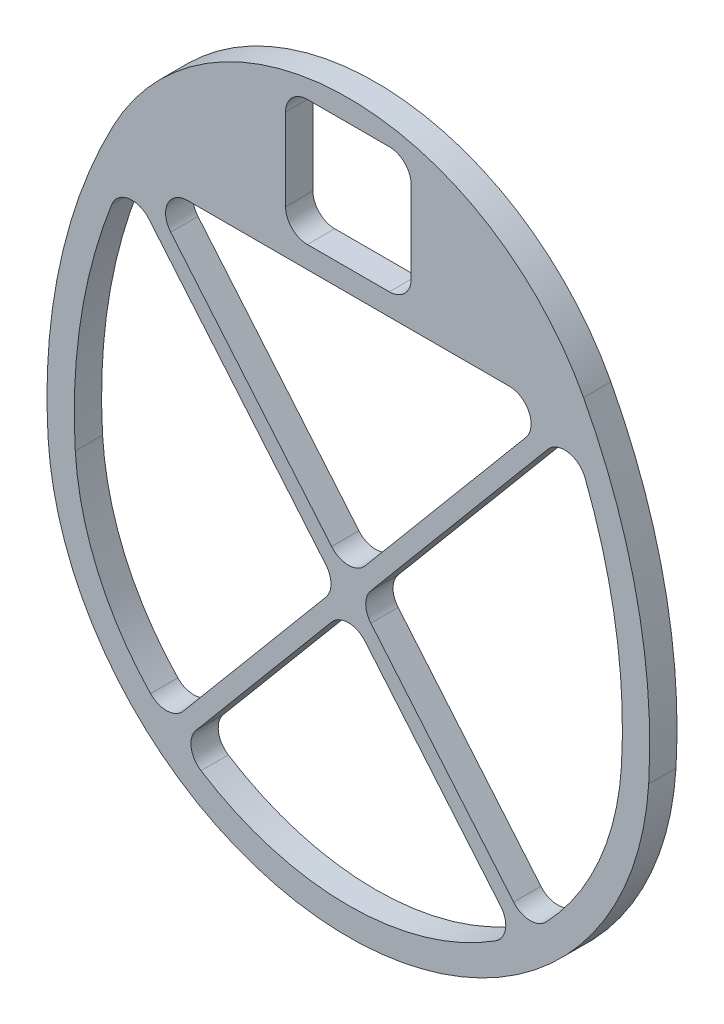
SolidWorks part; units mm, degrees
material "Balsa"
ref_plane "Front Plane" through (0, 0, 0) normal (0, 0, 1) x (1, 0, 0)
ref_plane "Top Plane" through (0, 0, 0) normal (0, 1, 0) x (1, 0, 0)
ref_plane "Right Plane" through (0, 0, 0) normal (1, 0, 0) x (0, 0, -1)
sketch "Sketch1" plane through (0, 0, 0) normal (0, 0, 1) x (1, 0, 0)
  line L8 (-63.5, 0) -> (63.5, 0) construction
  line L9 (-54.6952, 69.85) -> (54.6952, 69.85)
  line L10 (-50.8, 63.5) -> (50.8, 63.5)
  line L21 (-69.8384, -0.3833) -> (-63.5, 0)
  line L22 (63.5, 0) -> (69.8384, -0.3833)
  arc A0 (50.8, 63.5) -> (63.5, 0) centre (-63.2684, 7.6663) cw
  arc A1 (-50.8, 63.5) -> (-63.5, 0) centre (63.2684, 7.6663) ccw
  arc A2 (-54.6952, 69.85) -> (-69.8384, -0.3833) centre (63.2684, 7.6663) ccw
  arc A3 (54.6952, 69.85) -> (69.8384, -0.3833) centre (-63.2684, 7.6663) cw
  arc A4 (-56.5034, 66.2917) -> (-69.8384, -0.3833) centre (63.2684, 7.6663) ccw construction
  arc A5 (56.5034, 66.2917) -> (69.8384, -0.3833) centre (-63.2684, 7.6663) cw construction
  arc A6 (50.8, 63.5) -> (63.5, 0) centre (-63.2684, 7.6663) cw construction
  arc A7 (-50.8, 63.5) -> (-63.5, 0) centre (63.2684, 7.6663) ccw construction
  arc A8 (-54.6952, 69.85) -> (54.6952, 69.85) centre (0, 41.0178) cw
  arc A9 (-63.5, 0) -> (63.5, 0) centre (0, 3.8402) ccw
  arc A10 (-69.8384, -0.3833) -> (69.8384, -0.3833) centre (0, 3.8402) ccw
  point P0 (0, 0)
  point P13 (0, 63.5)
  dimension "D7" = 127
  dimension "D2" = 127
  dimension "D3" = 63.5
  dimension "D6" = 101.6
  dimension "D1" = 6.35
  dimension "D4" = 6.35
  dimension "D5" = 6.35
extrude "Boss-Extrude1" add sketch "Sketch1" along normal blind 6.35
sketch "Sketch2" plane through (0, 0, 6.35) normal (0, 0, 1) x (1, 0, 0)
  line L0 (0, 63.5) -> (0, 102.8471) construction
  line L1 (-14.605, 97.7785) -> (14.605, 97.7785)
  line L2 (-14.605, 97.7785) -> (-14.605, 68.5685)
  line L3 (-14.605, 68.5685) -> (14.605, 68.5685)
  line L4 (14.605, 97.7785) -> (14.605, 68.5685)
  line L5 (-14.605, 97.7785) -> (14.605, 68.5685) construction
  line L6 (-14.605, 68.5685) -> (14.605, 97.7785) construction
  line L7 (-50.8, 63.5) -> (50.8, 63.5) construction
  arc A0 (54.6952, 69.85) -> (-54.6952, 69.85) centre (0, 41.0178) ccw construction
  point P0 (0, 83.1735)
  point P15 (0, 83.1735)
  dimension "D1" = 29.21
  dimension "D2" = 29.21
extrude "Cut-Extrude1" cut sketch "Sketch2" against normal up to next
fillet "Fillet1" radius 5.08 4 edges at (14.605, 68.5685, 3.175) (14.605, 97.7785, 3.175) (-14.605, 97.7785, 3.175) (-14.605, 68.5685, 3.175)
sketch "Sketch3" plane through (0, 0, 6.35) normal (0, 0, 1) x (1, 0, 0)
  line L0 (-52.2593, 62.2755) -> (-49.3407, 64.7245)
  line L1 (-52.2593, 62.2755) -> (40.8035, -48.6324)
  line L2 (-49.3407, 64.7245) -> (43.7221, -46.1834)
  line L3 (40.8035, -48.6324) -> (43.7221, -46.1834)
  line L4 (49.3407, 64.7245) -> (52.2593, 62.2755)
  line L5 (49.3407, 64.7245) -> (-43.7221, -46.1834)
  line L6 (52.2593, 62.2755) -> (-40.8035, -48.6324)
  line L7 (-43.7221, -46.1834) -> (-40.8035, -48.6324)
  line L8 (-50.8, 63.5) -> (50.8, 63.5) construction
  point P0 (50.8, 63.5)
  point P7 (-50.8, 63.5)
  arc M17 (63.5, 0) -> (-63.5, 0) centre (0, 3.8402) cw
  arc M18 (-63.5, 0) -> (-50.8, 63.5) centre (63.2684, 7.6663) cw
  line M19 (-50.8, 63.5) -> (50.8, 63.5)
  arc M20 (50.8, 63.5) -> (63.5, 0) centre (-63.2684, 7.6663) cw
  dimension "D1" = 3.81
  dimension "D2" = 3.81
  dimension "D3" = 50
  dimension "D4" = 50
  dimension "D5" = 144.78
  dimension "D6" = 144.78
extrude "Boss-Extrude2" add sketch "Sketch3" against normal up to surface (6.35 mm away) contours L6 L5 L2 M20 M19 | L5 L2 L1 M19 M18 | L6 L2 L5 L1 | L2 L6 L1 M17 | L6 L1 L5 M17 up to face at (0, 83.1735, 0)
fillet "Fillet2" radius 5.08 12 edges at (48.3132, 63.5, 3.175) (-48.3132, 63.5, 3.175) (-2.4868, 2.9589, 3.175) (-41.9079, -44.0213, 3.175) (-51.7041, 61.6138, 3.175) (2.4868, 2.9589, 3.175) (51.7041, 61.6138, 3.175) (41.9079, -44.0213, 3.175) (0, -0.0047, 3.175) (38.9675, -46.4444, 3.175) (-38.9675, -46.4444, 3.175) (0, 5.9226, 3.175)
